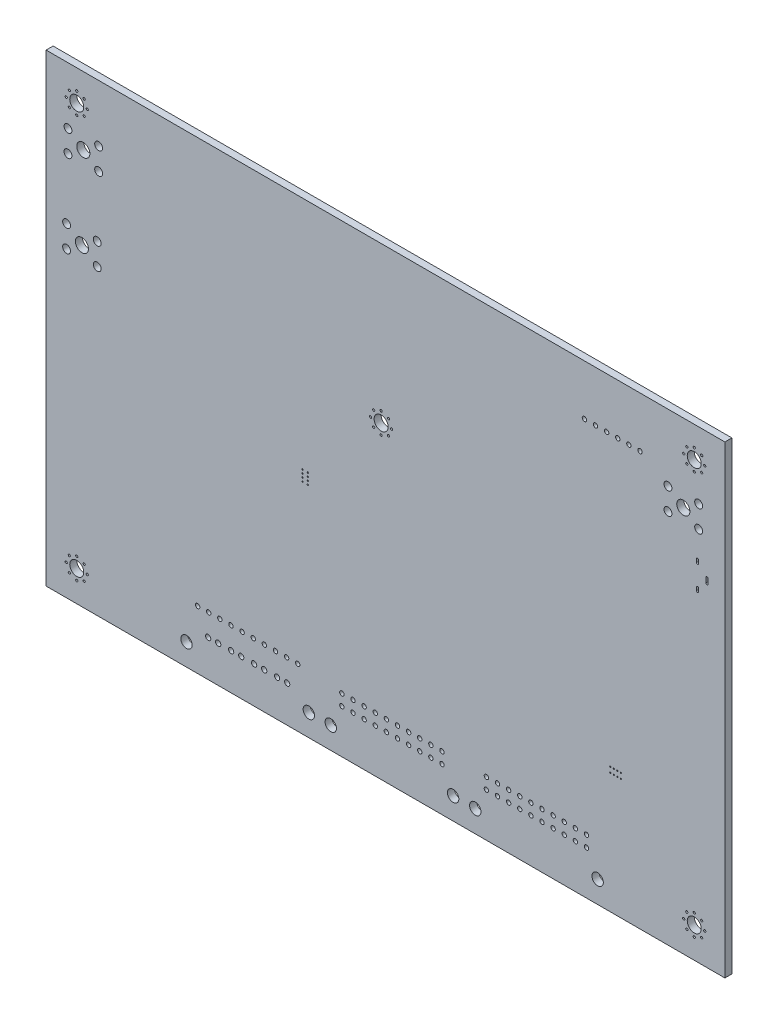
SolidWorks part; units mm, degrees
ref_plane "Front Plane" through (0, 0, 0) normal (0, 0, 1) x (1, 0, 0)
ref_plane "Top Plane" through (0, 0, 0) normal (0, 1, 0) x (1, 0, 0)
ref_plane "Right Plane" through (0, 0, 0) normal (1, 0, 0) x (0, 0, -1)
ref_plane "Plane1" through (0, 0, 1.6) normal (0, 0, 1) x (1, 0, 0)
sketch "Sketch1" plane through (0, 0, 1.6) normal (0, 0, 1) x (1, 0, 0)
  line L0 (143.65, 68.95) -> (143.65, 70.05)
  line L1 (144.15, 70.05) -> (144.15, 68.95)
  line L2 (141.5, 66.35) -> (141.5, 67.05)
  line L3 (142, 67.05) -> (142, 66.35)
  line L4 (141.5, 71.95) -> (141.5, 72.65)
  line L5 (142, 72.65) -> (142, 71.95)
  line L6 (-7, -7) -> (148, -7)
  line L7 (148, -7) -> (148, 99)
  line L8 (148, 99) -> (-7, 99)
  line L9 (-7, 99) -> (-7, -7)
  line L10 (-2, 86) -> (5, 81) construction
  line L11 (-2.32, 67.02) -> (4.68, 62.02) construction
  line L12 (135, 83.75) -> (142, 78.75) construction
  circle A0 centre (0, 94.4) radius 0.25
  circle A1 centre (141, 94.4) radius 0.25
  arc A2 (143.65, 70.05) -> (144.15, 70.05) centre (143.9, 70.05) cw
  arc A3 (144.15, 68.95) -> (143.65, 68.95) centre (143.9, 68.95) cw
  circle A4 centre (143.4, 92) radius 0.25
  circle A5 centre (143.4, 0) radius 0.25
  circle A6 centre (0, 89.6) radius 0.25
  circle A7 centre (141, 89.6) radius 0.25
  circle A8 centre (2.4, 92) radius 0.25
  circle A9 centre (1.6971, 90.3029) radius 0.25
  circle A10 centre (0, 92) radius 1.6
  circle A11 centre (-1.6971, 90.3029) radius 0.25
  circle A12 centre (1.6971, 93.6971) radius 0.25
  circle A13 centre (-1.6971, 93.6971) radius 0.25
  circle A14 centre (-2.4, 92) radius 0.25
  circle A15 centre (138.6, 92) radius 0.25
  circle A16 centre (142.6971, 93.6971) radius 0.25
  circle A17 centre (139.3029, 93.6971) radius 0.25
  circle A18 centre (142.6971, 90.3029) radius 0.25
  circle A19 centre (139.3029, 90.3029) radius 0.25
  circle A20 centre (141, 92) radius 1.6
  arc A21 (142, 66.35) -> (141.5, 66.35) centre (141.75, 66.35) cw
  arc A22 (141.5, 67.05) -> (142, 67.05) centre (141.75, 67.05) cw
  arc A23 (142, 71.95) -> (141.5, 71.95) centre (141.75, 71.95) cw
  arc A24 (141.5, 72.65) -> (142, 72.65) centre (141.75, 72.65) cw
  circle A25 centre (142, 83.75) radius 0.9
  circle A26 centre (142, 78.75) radius 0.9
  circle A27 centre (135, 83.75) radius 0.9
  circle A28 centre (135, 78.75) radius 0.9
  circle A29 centre (126.08, 87.5) radius 0.5
  circle A30 centre (128.62, 87.5) radius 0.5
  circle A31 centre (51.555, 44.534) radius 0.15
  circle A32 centre (51.555, 43.734) radius 0.15
  circle A33 centre (51.555, 42.934) radius 0.15
  circle A34 centre (51.555, 45.334) radius 0.15
  circle A35 centre (5, 86) radius 0.9
  circle A36 centre (4.68, 67.02) radius 0.9
  circle A37 centre (4.68, 62.02) radius 0.9
  circle A38 centre (5, 81) radius 0.9
  circle A39 centre (-2, 81) radius 0.9
  circle A40 centre (-2, 86) radius 0.9
  circle A41 centre (-2.32, 67.02) radius 0.9
  circle A42 centre (-2.32, 62.02) radius 0.9
  circle A43 centre (52.755, 42.934) radius 0.15
  circle A44 centre (67.1, 63.5) radius 0.25
  circle A45 centre (52.755, 45.334) radius 0.15
  circle A46 centre (52.755, 43.734) radius 0.15
  circle A47 centre (52.755, 44.534) radius 0.15
  circle A48 centre (118.46, 87.5) radius 0.5
  circle A49 centre (121, 87.5) radius 0.5
  circle A50 centre (115.92, 87.5) radius 0.5
  circle A51 centre (71.9, 63.5) radius 0.25
  circle A52 centre (69.5, 65.9) radius 0.25
  circle A53 centre (69.5, 61.1) radius 0.25
  circle A54 centre (71.1971, 65.1971) radius 0.25
  circle A55 centre (67.8029, 65.1971) radius 0.25
  circle A56 centre (67.8029, 61.8029) radius 0.25
  circle A57 centre (69.5, 63.5) radius 1.6
  circle A58 centre (71.1971, 61.8029) radius 0.25
  circle A59 centre (122.65, 21.7) radius 0.15
  circle A60 centre (121.85, 21.7) radius 0.15
  circle A61 centre (123.45, 21.7) radius 0.15
  circle A62 centre (124.25, 21.7) radius 0.15
  circle A63 centre (123.54, 87.5) radius 0.5
  circle A64 centre (-2.4, 0) radius 0.25
  circle A65 centre (121.85, 20.5) radius 0.15
  circle A66 centre (123.45, 20.5) radius 0.15
  circle A67 centre (124.25, 20.5) radius 0.15
  circle A68 centre (122.65, 20.5) radius 0.15
  circle A69 centre (27.6, 6.36) radius 0.5
  circle A70 centre (30.14, 6.36) radius 0.5
  circle A71 centre (37.76, 6.36) radius 0.5
  circle A72 centre (35.22, 6.36) radius 0.5
  circle A73 centre (32.68, 6.36) radius 0.5
  circle A74 centre (45.38, 6.36) radius 0.5
  circle A75 centre (42.84, 6.36) radius 0.5
  circle A76 centre (40.3, 6.36) radius 0.5
  circle A77 centre (47.92, 6.36) radius 0.5
  circle A78 centre (108.78, 5.54) radius 0.5
  circle A79 centre (111.32, 5.54) radius 0.5
  circle A80 centre (113.86, 5.54) radius 0.5
  circle A81 centre (116.4, 5.54) radius 0.5
  circle A82 centre (80.86, 5.54) radius 0.5
  circle A83 centre (83.4, 5.54) radius 0.5
  circle A84 centre (93.54, 5.54) radius 0.5
  circle A85 centre (98.62, 5.54) radius 0.5
  circle A86 centre (96.08, 5.54) radius 0.5
  circle A87 centre (101.16, 5.54) radius 0.5
  circle A88 centre (103.7, 5.54) radius 0.5
  circle A89 centre (106.24, 5.54) radius 0.5
  circle A90 centre (73.24, 5.54) radius 0.5
  circle A91 centre (75.78, 5.54) radius 0.5
  circle A92 centre (78.32, 5.54) radius 0.5
  circle A93 centre (68.16, 5.54) radius 0.5
  circle A94 centre (70.7, 5.54) radius 0.5
  circle A95 centre (65.62, 5.54) radius 0.5
  circle A96 centre (50.46, 6.36) radius 0.5
  circle A97 centre (60.54, 5.54) radius 0.5
  circle A98 centre (63.08, 5.54) radius 0.5
  circle A99 centre (-1.6971, -1.6971) radius 0.25
  circle A100 centre (0, 0) radius 1.6
  circle A101 centre (-1.6971, 1.6971) radius 0.25
  circle A102 centre (73.24, 3) radius 0.5
  circle A103 centre (91, -2) radius 1.3
  circle A104 centre (85.94, -2) radius 1.3
  circle A105 centre (106.24, 3) radius 0.5
  circle A106 centre (108.78, 3) radius 0.5
  circle A107 centre (93.54, 3) radius 0.5
  circle A108 centre (98.62, 3) radius 0.5
  circle A109 centre (96.08, 3) radius 0.5
  circle A110 centre (101.16, 3) radius 0.5
  circle A111 centre (103.7, 3) radius 0.5
  circle A112 centre (83.4, 3) radius 0.5
  circle A113 centre (80.86, 3) radius 0.5
  circle A114 centre (78.32, 3) radius 0.5
  circle A115 centre (75.78, 3) radius 0.5
  circle A116 centre (111.32, 3) radius 0.5
  circle A117 centre (141, -2.4) radius 0.25
  circle A118 centre (118.94, -2) radius 1.3
  circle A119 centre (116.4, 3) radius 0.5
  circle A120 centre (113.86, 3) radius 0.5
  circle A121 centre (141, 2.4) radius 0.25
  circle A122 centre (138.6, 0) radius 0.25
  circle A123 centre (139.3029, -1.6971) radius 0.25
  circle A124 centre (142.6971, 1.6971) radius 0.25
  circle A125 centre (142.6971, -1.6971) radius 0.25
  circle A126 centre (139.3029, 1.6971) radius 0.25
  circle A127 centre (141, 0) radius 1.6
  circle A128 centre (58, -2) radius 1.3
  circle A129 centre (63.08, 3) radius 0.5
  circle A130 centre (60.54, 3) radius 0.5
  circle A131 centre (68.16, 3) radius 0.5
  circle A132 centre (65.62, 3) radius 0.5
  circle A133 centre (70.7, 3) radius 0.5
  circle A134 centre (42.805, 1.36) radius 0.6
  circle A135 centre (45.755, 1.36) radius 0.6
  circle A136 centre (40.505, 1.36) radius 0.6
  circle A137 centre (37.555, 1.36) radius 0.6
  circle A138 centre (48.055, 1.36) radius 0.6
  circle A139 centre (53, -2) radius 1.3
  circle A140 centre (30.005, 1.36) radius 0.6
  circle A141 centre (32.305, 1.36) radius 0.6
  circle A142 centre (35.255, 1.36) radius 0.6
  circle A143 centre (25.06, -2) radius 1.3
  circle A144 centre (2.4, 0) radius 0.25
  circle A145 centre (1.6971, -1.6971) radius 0.25
  circle A146 centre (0, -2.4) radius 0.25
  circle A147 centre (1.6971, 1.6971) radius 0.25
  circle A148 centre (0, 2.4) radius 0.25
  circle A149 centre (138.5, 81.25) radius 1.5
  circle A150 centre (1.5, 83.5) radius 1.5
  circle A151 centre (1.18, 64.52) radius 1.5
  dimension "D1" = 3
extrude "Boss-Extrude1" add sketch "Sketch1" against normal blind 1.6
